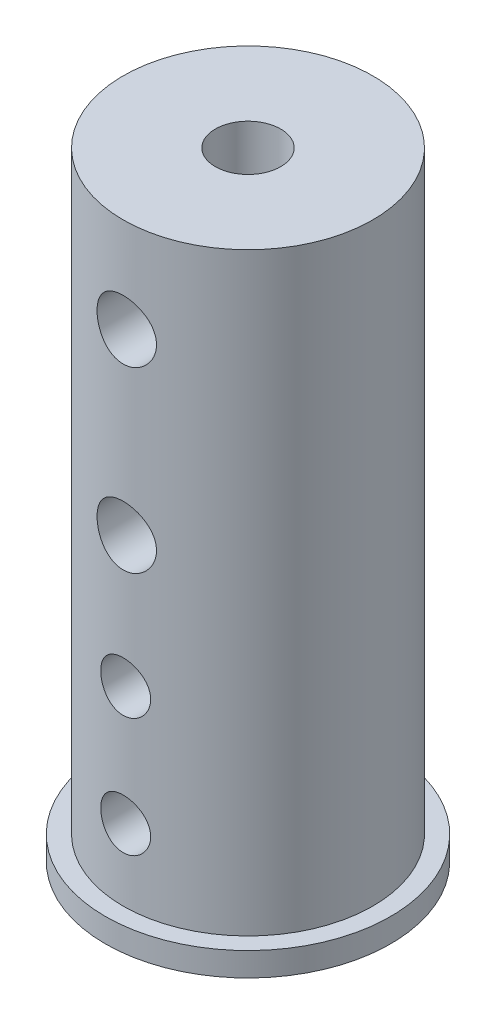
SolidWorks part; units mm, degrees
ref_plane "Спереди" through (0, 0, 0) normal (0, 0, 1) x (1, 0, 0)
ref_plane "Сверху" through (0, 0, 0) normal (0, 1, 0) x (1, 0, 0)
ref_plane "Справа" through (0, 0, 0) normal (1, 0, 0) x (0, 0, -1)
sketch "Эскиз1" plane through (0, 0, 0) normal (0, 1, 0) x (1, 0, 0)
  circle A0 centre (0, 0) radius 12
  circle A1 centre (0, 0) radius 2.75
  dimension "D1" = 24
  dimension "D2" = 5.5
extrude "Бобышка-Вытянуть1" add sketch "Эскиз1" along normal blind 2
sketch "Эскиз2" plane through (0, 2, 0) normal (0, 1, 0) x (1, 0, 0)
  line L0 (0, 13.8) -> (0, 0) construction
  circle A0 centre (0, 0) radius 2.75
  circle A1 centre (0, 0) radius 10.5
  point P3 (-2.3844, 9.8742)
  point P14 (0, 0)
  dimension "D1" = 10.5
  dimension "D2" = 5.5
  dimension "D4" = 13.8
extrude "Бобышка-Вытянуть2" add sketch "Эскиз2" along normal blind 50
hole_wizard "Отверстие обработанное метчиком M51" positions "Эскиз6" profile "Эскиз7" tap size "M5" standard "ISO"
sketch "Эскиз6" plane through (0, 0, 0) normal (0, 0, 1) x (1, 0, 0)
  line L0 (0, 0) -> (0, 52) construction
  line L1 (-12, 0) -> (12, 0) construction
  line L2 (10.5, 52) -> (-10.5, 52) construction
  point P0 (0, 8)
  point P2 (0, 18)
  point P12 (0, 20.9682)
  point P13 (0, 10.7265)
  dimension "D1" = 8
  dimension "D2" = 10
sketch "Эскиз7" plane through (0, 8, 0) normal (1, 0, 0) x (0, 1, 0)
  line L0 (0, 0) -> (0, 10.5)
  line L1 (0, 10.5) -> (2.1, 10.5)
  line L2 (2.1, 10.5) -> (2.1, 0)
  line L5 (2.1, 0) -> (0, 0)
  line L11 (0, -6.35) -> (0, 107.95) construction
  dimension "Диаметр проходного сверла" = 4.2
  dimension "Глубина проходного сверла" = 10.5
cosmetic thread "Отверстие резьбы1" parameters "D2"=5
cosmetic thread "Отверстие резьбы2" parameters "D2"=5
hole_wizard "Отверстие обработанное метчиком M61" positions "Эскиз8" profile "Эскиз9" tap size "M6" standard "ISO"
sketch "Эскиз8" plane through (0, 0, 0) normal (0, 0, 1) x (1, 0, 0)
  line L0 (0, 52) -> (0, 0) construction
  line L1 (10.5, 52) -> (-10.5, 52) construction
  point P0 (0, 44)
  point P2 (0, 29)
  point P11 (0, 44.3905)
  point P12 (0, 30.2303)
  dimension "D1" = 15
  dimension "D2" = 8
sketch "Эскиз9" plane through (0, 44, 0) normal (1, 0, 0) x (0, 1, 0)
  line L0 (0, 0) -> (0, 12)
  line L1 (0, 12) -> (2.5, 12)
  line L2 (2.5, 12) -> (2.5, 0)
  line L5 (2.5, 0) -> (0, 0)
  line L11 (0, -6.35) -> (0, 107.95) construction
  dimension "Диаметр проходного сверла" = 5
  dimension "Глубина проходного сверла" = 12
cosmetic thread "Отверстие резьбы3" parameters "D2"=6
cosmetic thread "Отверстие резьбы4" parameters "D2"=6
